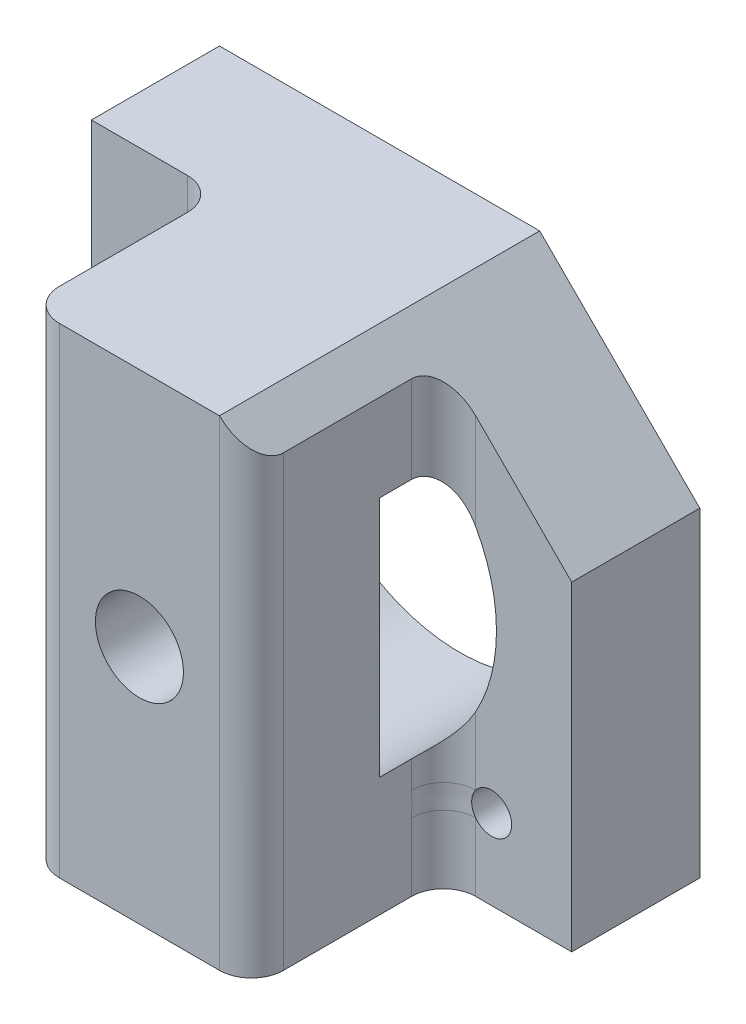
SolidWorks part; units mm, degrees
ref_plane "Front Plane" through (0, 0, 0) normal (0, 0, 1) x (1, 0, 0)
ref_plane "Top Plane" through (0, 0, 0) normal (0, 1, 0) x (1, 0, 0)
ref_plane "Right Plane" through (0, 0, 0) normal (1, 0, 0) x (0, 0, -1)
sketch "Sketch1" plane through (0, 0, 0) normal (0, 0, 1) x (1, 0, 0)
  line L0 (-15, -15) -> (5, -15)
  line L1 (5, -15) -> (15, -5)
  line L2 (-15, -15) -> (-15, 15)
  line L3 (-15, 15) -> (15, 15)
  line L4 (15, -5) -> (15, 15)
  line L5 (-15, -15) -> (15, 15) construction
  line L6 (-15, 15) -> (15, -15) construction
  circle A0 centre (-10, 10) radius 1.25
  circle A1 centre (10, 10) radius 1.25
  circle A2 centre (-10, -10) radius 1.25
  point P0 (0, 0)
  point P11 (0, 0)
  point P14 (0, 0)
  dimension "D3" = 2.5
  dimension "D6" = 20
  dimension "D1" = 30
  dimension "D2" = 30
  dimension "D4" = 20
  dimension "D5" = 135
extrude "Main" add sketch "Sketch1" along normal blind 20
sketch "Sketch2" plane through (0, 0, 0) normal (0, 0, 1) x (1, 0, 0)
  line L0 (-15, -15) -> (15, 15) construction
  line L1 (-15, 15) -> (15, -15) construction
  line L2 (15, -5) -> (15, 15) construction
  line L3 (15, 15) -> (-15, 15) construction
  circle A0 centre (0, 0) radius 10.3
  dimension "D1" = 20.6
extrude "CentralHole" cut sketch "Sketch2" along normal blind 12
sketch "Sketch5" plane through (0, 0, 20) normal (0, 0, 1) x (1, 0, 0)
  line L0 (15, 15) -> (-15, 15) construction
  line L1 (15, -15) -> (7, -15)
  line L2 (15, -15) -> (15, 15)
  line L3 (15, 15) -> (7, 15)
  line L4 (7, -15) -> (7, 15)
  line L5 (-15, -15) -> (5, -15) construction
  line L6 (-15, -15) -> (-7, -15)
  line L7 (-15, -15) -> (-15, 15)
  line L8 (-15, 15) -> (-7, 15)
  line L9 (-7, -15) -> (-7, 15)
  line L10 (15, -5) -> (15, 15) construction
  circle A0 centre (0, 0) radius 2.75
  dimension "D3" = 5.5
  dimension "D1" = 8
  dimension "D2" = 8
extrude "Cut-Extrude3" cut sketch "Sketch5" against normal blind 12
fillet "Fillet1" radius 2 6 edges at (-7, 0, 20) (7, 1, 20) (-7, 11.2779, 8) (-7, -11.2779, 8) (7, 11.2779, 8) (7, -10.2779, 8)
ref_plane "Plane1" through (0, 20, 0) normal (0, 1, 0) x (1, 0, 0)
mirror "Mirror1" about plane through (0, 20, 0) normal (0, 1, 0) of bodies 104
sketch "Sketch6" plane through (0, 0, 20) normal (0, 0, 1) x (1, 0, 0)
  line L0 (15, -5) -> (15, 15) construction
  line L1 (-15, 15) -> (15, 15)
  line L2 (-15, 15) -> (-15, -15)
  line L3 (-15, -15) -> (15, -15)
  line L4 (15, 15) -> (15, -15)
  line L5 (-15, 15) -> (-15, -15) construction
  line L6 (-15, -15) -> (-9, -15) construction
  point P5 (15, 15)
  point P8 (-15, -15)
  point P11 (-15, -15)
extrude "Cut-Extrude4" cut sketch "Sketch6" against normal through all
